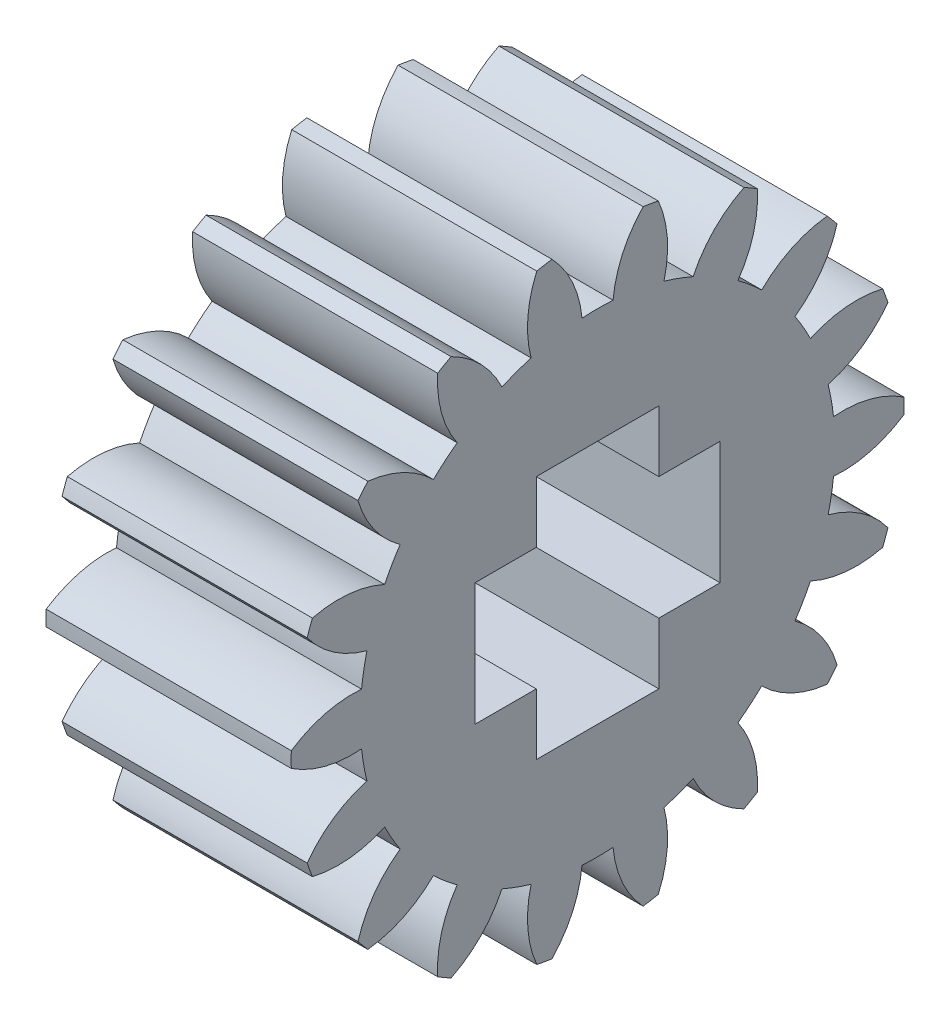
SolidWorks part; units mm, degrees
ref_plane "Plane1" through (0, 0, 0) normal (0, 0, 1) x (1, 0, 0)
ref_plane "Plane2" through (0, 0, 0) normal (0, 1, 0) x (1, 0, 0)
ref_plane "Plane3" through (0, 0, 0) normal (1, 0, 0) x (0, 0, -1)
sketch "HoldingSke" plane through (0, 0, 0) normal (0, 1, 0) x (1, 0, 0)
  line L0 (0, 0) -> (0.634, -0.206)
  line L1 (-15, 0) -> (100, 0) construction
  line L2 (0, 0) -> (-2.1039, 2.3779)
  line L3 (0, 0) -> (-11.863, 4.5341)
  line L4 (0, 0) -> (8.2133, 2.6687)
  line L5 (0, 0) -> (-46.8476, -17.4728)
  line L6 (0, 0) -> (-9.9476, -6.7116)
  line L7 (-2.1039, 2.3779) -> (8.6586, 51.2059)
  line L8 (-76.2, 54.61) -> (-75.5, 54.61)
  line L9 (-71.009, 38.7566) -> (-53.1078, 45.2721)
  line L10 (-76.2, 71.12) -> (104.1128, 71.12)
  line L11 (0, 0) -> (-12, 0)
  line L12 (-76.2, 101.6) -> (-76.147, 101.6)
  line L13 (24.9733, 27.94) -> (52.9518, 28.4284)
  line L14 (24.9733, 27.94) -> (24.9743, 27.94)
  line L15 (24.9733, 27.94) -> (100.4006, 29.5858)
  line L16 (-63.627, -1.5) -> (-12.827, -1.5)
  circle A0 centre (0, 0) radius 2
  circle A1 centre (0, 0) radius 11.624
  circle A2 centre (0, 0) radius 37.5
  circle A3 centre (0, 0) radius 2
  dimension "MHD" = 23.248
  dimension "Hub_dia" = 75
  dimension "Bore" = 4
  dimension "MBD" = 4
  dimension "Num_teeth" = 18
  dimension "Pitch" = 0.6667
  dimension "Overall_len" = 50
  dimension "Show_teeth" = 18
  dimension "Thickness" = 12
  dimension "OAL" = 50.0001
  dimension "T_dim" = 0.7
  dimension "Ap" = 20
  dimension "H" = 19.05
  dimension "Pitch_radius" = 180.3128
  dimension "Width" = 12
  dimension "Backlash" = 0.053
  dimension "Addendum_fac" = 1
  dimension "Dedendum_fac" = 1.25
  dimension "Clearance_fac" = 0.25
  dimension "Dedendum_add" = 0.001
  dimension "Module" = 1.5
sketch "BasProSke" plane through (0, 0, 0) normal (0, 1, 0) x (1, 0, 0)
  line L0 (-10, 0) -> (60, 0) construction
  line L1 (0, 0) -> (0, 15)
  line L2 (0, 0) -> (12, 0)
  line L3 (12, 0) -> (12, 15)
  line L4 (12, 15) -> (0, 15)
  dimension "Thickness" = 12
  dimension "Diameter" = 30
revolve "Base-Revolve" add sketch "BasProSke" angle 360 about L0
sketch "TooCutSke" plane through (0, 0, 0) normal (1, 0, 0) x (0, 0, -1)
  line L1 (0, 0) -> (0, 107) construction
  line L2 (0, 0) -> (-1.2693, 13.4402) construction
  line L3 (0, 0) -> (-4.6734, 26.504) construction
  line L4 (-1.2693, 13.4402) -> (-2.3367, 13.252) construction
  arc A0 (0.76, 11.5991) -> (-0.76, 11.5991) centre (0, 0) ccw
  arc A1 (2.2542, 14.8553) -> (-2.2542, 14.8553) centre (0, 0) ccw
  circle A2 centre (0, 0) radius 13.5 construction
  circle A3 centre (0, 0) radius 12.6859 construction
  arc A4 (-0.76, 11.5991) -> (-2.2542, 14.8553) centre (-6.1371, 11.1026) ccw
  arc A5 (2.2542, 14.8553) -> (0.76, 11.5991) centre (6.1371, 11.1026) ccw
  dimension "Root_dia" = 23.248
  dimension "Overcut_dia" = 30.0508
  dimension "Pitch_dia" = 27
  dimension "Base_dia" = 25.3717
  dimension "Flank_rad" = 5.4
  dimension "Half_ang" = 10
  dimension "Half_CT" = 1.0839
extrude "ToothCut" cut sketch "TooCutSke" along normal through all
fillet "Breaks" [suppressed] radius 0.03
fillet "RootFillets" [suppressed] radius 0.376
pattern_circular "TeethCuts" count 18 every 20 about axis through (-10, 0, 0) along (1, 0, 0) of "ToothCut", "RootFillets", "Breaks"
sketch "HubNeaOneSke" plane through (0, 0, 0) normal (-1, 0, 0) x (0, 0, 1)
  circle A0 centre (0, 0) radius 11.624
  dimension "Diameter" = 23.248
extrude "HubNearOne" [suppressed] add sketch "HubNeaOneSke" along normal blind 38.0001
sketch "HubNeaBotSke" plane through (0, 0, 0) normal (-1, 0, 0) x (0, 0, 1)
  circle A0 centre (0, 0) radius 11.624
  dimension "Diameter" = 23.248
extrude "HubNearBoth" [suppressed] add sketch "HubNeaBotSke" along normal blind 19
ref_plane "FarPln" through (12, 0, 0) normal (1, 0, 0) x (0, 0, -1)
sketch "HubFarSke" plane through (12, 0, 0) normal (1, 0, 0) x (0, 0, -1)
  circle A0 centre (0, 0) radius 11.624
  dimension "Diameter" = 23.248
extrude "HubFar" [suppressed] add sketch "HubFarSke" along normal blind 19
sketch "BorSke" plane through (0, 0, 0) normal (1, 0, 0) x (0, 0, -1)
  circle A0 centre (0, 0) radius 2
  dimension "Diameter" = 4
extrude "Bore" cut sketch "BorSke" along normal mid plane 100.0001
sketch "KeySke" plane through (0, 0, 0) normal (1, 0, 0) x (0, 0, -1)
  line L0 (-0.8, 0) -> (-0.8, 2.7)
  line L1 (-0.8, 2.7) -> (0.8, 2.7)
  line L2 (0.8, 2.7) -> (0.8, 0)
  line L3 (0, 0) -> (0, 34) construction
  line L4 (-0.8, 0) -> (0.8, 0)
  dimension "Offset" = 2.7
  dimension "Width" = 1.6
extrude "Keyway" [suppressed] cut sketch "KeySke" along normal mid plane 100.0001
pattern_circular "Keyway2" [suppressed] count 2 every 90 about axis through (-10, 0, 0) along (1, 0, 0)
sketch "Sketch2" plane through (12, 0, 0) normal (1, 0, 0) x (0, 0, -1)
  line L1 (3, -6) -> (-3, -6)
  line L2 (3, -6) -> (3, 6)
  line L3 (3, 6) -> (-3, 6)
  line L4 (-3, -6) -> (-3, 6)
  line L5 (3, -6) -> (-3, 6) construction
  line L6 (3, 6) -> (-3, -6) construction
  line L7 (6, -3) -> (-6, -3)
  line L8 (6, -3) -> (6, 3)
  line L9 (6, 3) -> (-6, 3)
  line L10 (-6, -3) -> (-6, 3)
  line L11 (6, -3) -> (-6, 3) construction
  line L12 (6, 3) -> (-6, -3) construction
  point P0 (0, 0)
  point P6 (0, 0)
  dimension "D1" = 12
  dimension "D2" = 6
  dimension "D3" = 12
  dimension "D4" = 6
extrude "Cut-Extrude2" cut sketch "Sketch2" against normal blind 16 contours L10 L7 L4 L9 | L9 L2 L3 L4 | L2 L9 L4 L7 | L8 L9 L2 L7 | L2 L7 L4 L1
equation "' \"Module@HoldingSke\" = 6.35"
equation "' \"Num_teeth@HoldingSke\" = 12"
equation "' \"Ap@HoldingSke\" =  20"
equation "' \"Ap@HoldingSke\" = 20"
equation "' \"Width@HoldingSke\" = 0.5 * 25.4"
equation "' \"Hub_dia@HoldingSke\"= 1 * 25.4"
equation "' \"Hub_dia@HoldingSke\" = 1 * 25.4"
equation "' \"Overall_len@HoldingSke\" = 1.0 * 25.4"
equation "' \"Bore@HoldingSke\" = 0.75 * 25.4"
equation "' \"T_dim@HoldingSke\" = 0.1 * 25.4"
equation "' \"Width@KeySke\" = 0.25 * 25.4"
equation "' \"Show_teeth@HoldingSke\" = 13"
equation "' \"Backlash@HoldingSke\" = 0.009 * 25.4"
equation "' \"Addendum_fac@HoldingSke\" = 1.0"
equation "' \"Dedendum_fac@HoldingSke\" = 1.25"
equation "' \"Dedendum_add@HoldingSke\" = 0.00005 * 25.4"
equation "' \"Clearance_fac@HoldingSke\" = 0.25"
equation "\"Pitch@HoldingSke\" = 1 / \"Module@HoldingSke\""
equation "\"Overcut_dia@TooCutSke\" = (\"Num_teeth@HoldingSke\" + 2 * \"Addendum_fac@HoldingSke\") / \"Pitch@HoldingSke\" + 0.002 * 25.4"
equation "\"Pitch_dia@TooCutSke\" = \"Num_teeth@HoldingSke\" / \"Pitch@HoldingSke\""
equation "\"Base_dia@TooCutSke\" = \"Num_teeth@HoldingSke\" / \"Pitch@HoldingSke\" * cos((\"Ap@HoldingSke\"  * 3.14159265 / 180))"
equation "\"Root_dia@TooCutSke\" = (\"Num_teeth@HoldingSke\" + 2) / \"Pitch@HoldingSke\" - 2 * (\"Addendum_fac@HoldingSke\" + \"Dedendum_fac@HoldingSke\") / \"Pitch@HoldingSke\" - \"Dedendum_add@HoldingSke\" * 2"
equation "\"Half_ang@TooCutSke\" = 180 / \"Num_teeth@HoldingSke\""
equation "\"Half_CT@TooCutSke\" = \"Num_teeth@HoldingSke\" / \"Pitch@HoldingSke\" * sin((3.14159265 / 2 / \"Num_teeth@HoldingSke\")) / 2 - 7 * \"Backlash@HoldingSke\" / 4"
equation "\"Flank_rad@TooCutSke\" = \"Num_teeth@HoldingSke\" / \"Pitch@HoldingSke\" / 5"
equation "\"Radius@RootFillets\" = \"Clearance_fac@HoldingSke\" / \"Pitch@HoldingSke\" + \"Dedendum_add@HoldingSke\""
equation "\"Break_rad@Breaks\" = 0.02 / \"Pitch@HoldingSke\""
equation "\"Thickness@HoldingSke\" = \"Width@HoldingSke\""
equation "\"OAL@HoldingSke\" = \"Thickness@HoldingSke\""
equation "\"MHD@HoldingSke\" = (\"Num_teeth@HoldingSke\" + 2) / \"Pitch@HoldingSke\" - 2 * (\"Addendum_fac@HoldingSke\" + \"Dedendum_fac@HoldingSke\")  / \"Pitch@HoldingSke\" - \"Dedendum_add@HoldingSke\" * 2"
equation "\"MBD@HoldingSke\" = (\"Num_teeth@HoldingSke\" + 2) / \"Pitch@HoldingSke\" - 2 * (\"Addendum_fac@HoldingSke\" + \"Dedendum_fac@HoldingSke\")  / \"Pitch@HoldingSke\" - \"Dedendum_add@HoldingSke\" * 2 - 0.002 * 25.4"
equation "\"MHD@HoldingSke\" = ((sgn( \"MHD@HoldingSke\" - \"Hub_dia@HoldingSke\" )-1)*( \"MHD@HoldingSke\" - \"Hub_dia@HoldingSke\" ))/-2+ \"Hub_dia@HoldingSke\""
equation "\"MBD@HoldingSke\" = ((sgn( \"MBD@HoldingSke\" - \"Bore@HoldingSke\" )-1)*( \"MBD@HoldingSke\" - \"Bore@HoldingSke\" ))/-2+ \"Bore@HoldingSke\""
equation "\"OAL@HoldingSke\" = ((sgn( \"OAL@HoldingSke\" - \"Overall_len@HoldingSke\" )+1)*( \"OAL@HoldingSke\" - \"Overall_len@HoldingSke\" ))/2 + \"Overall_len@HoldingSke\" + 0.000002 * 25.4"
equation "\"Num_teeth@TeethCuts\" = int( \"Show_teeth@HoldingSke\" ) + 1"
equation "\"Num_teeth@TeethCuts\" = ((sgn( \"Num_teeth@TeethCuts\" - \"Num_teeth@HoldingSke\" )-1)*( \"Num_teeth@TeethCuts\" - \"Num_teeth@HoldingSke\" ))/-2+ \"Num_teeth@HoldingSke\""
equation "\"Num_teeth@TeethCuts\" = ((sgn( \"Num_teeth@TeethCuts\" - 2.0)+1)*( \"Num_teeth@TeethCuts\" - 2.0))/2 +2.0"
equation "\"Angle@TeethCuts\" = 360.0 / \"Num_teeth@HoldingSke\""
equation "\"Diameter@BasProSke\" = (\"Num_teeth@HoldingSke\" + 2 * \"Addendum_fac@HoldingSke\") / \"Pitch@HoldingSke\""
equation "\"Thickness@BasProSke\"  = \"Thickness@HoldingSke\""
equation "' \"Fillet_rad@BasProSke\" =  \"Thickness@HoldingSke\" * 0.05"
equation "' \"Fillet_rad@BasProSke\" = \"Thickness@HoldingSke\" * 0.05"
equation "\"MHD@HoldingSke\" = ((sgn( \"MHD@HoldingSke\" - \"Root_dia@TooCutSke\" )-1)*( \"MHD@HoldingSke\" - \"Root_dia@TooCutSke\" ))/-2+ \"Root_dia@TooCutSke\""
equation "\"Diameter@HubNeaOneSke\" = \"MHD@HoldingSke\""
equation "\"Length@HubNearOne\" = \"OAL@HoldingSke\" - \"Thickness@BasProSke\""
equation "\"Diameter@HubNeaBotSke\" = \"MHD@HoldingSke\""
equation "\"Length@HubNearBoth\" = ( \"OAL@HoldingSke\" - \"Thickness@BasProSke\" ) / 2.0"
equation "\"Thickness@FarPln\" = \"Thickness@BasProSke\""
equation "\"Diameter@HubFarSke\" = \"MHD@HoldingSke\""
equation "\"Length@HubFar\" = ( \"OAL@HoldingSke\" - \"Thickness@BasProSke\" ) / 2.0"
equation "\"Diameter@BorSke\" = \"MBD@HoldingSke\""
equation "\"D1@Bore\" = \"OAL@HoldingSke\" * 2.0"
equation "\"D1@Keyway\" = \"OAL@HoldingSke\" * 2.0"
equation "\"Offset@KeySke\" = \"T_dim@HoldingSke\" + \"MBD@HoldingSke\" / 2.0"
